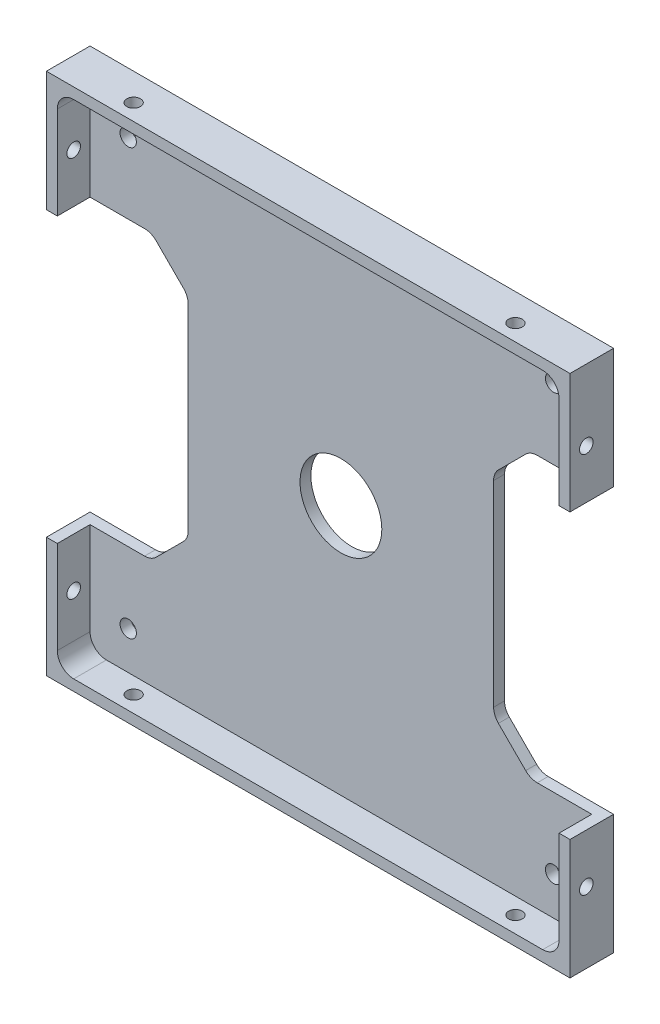
SolidWorks part; units mm, degrees
material "6061-T6 (SS)"
ref_plane "Front" through (0, 0, 0) normal (0, 0, 1) x (1, 0, 0)
ref_plane "Top" through (0, 0, 0) normal (0, 1, 0) x (1, 0, 0)
ref_plane "Right" through (0, 0, 0) normal (1, 0, 0) x (0, 0, -1)
sketch "Sketch1" plane through (0, 0, 0) normal (0, 0, 1) x (1, 0, 0)
  line L1 (-48, -48) -> (48, -48)
  line L2 (-48, -48) -> (-48, 48)
  line L3 (-48, 48) -> (48, 48)
  line L4 (48, -48) -> (48, 48)
  line L5 (-48, -48) -> (48, 48) construction
  line L6 (-48, 48) -> (48, -48) construction
  point P0 (0, 0)
  dimension "D1" = 96
  dimension "D2" = 96
extrude "Boss-Extrude1" add sketch "Sketch1" along normal blind 8
sketch "Sketch2" plane through (0, 0, 8) normal (0, 0, 1) x (1, 0, 0)
  line L1 (46, -46) -> (-46, -46)
  line L2 (46, -46) -> (46, 46)
  line L3 (46, 46) -> (-46, 46)
  line L4 (-46, -46) -> (-46, 46)
  line L5 (46, -46) -> (-46, 46) construction
  line L6 (46, 46) -> (-46, -46) construction
  point P0 (0, 0)
  dimension "D1" = 92
  dimension "D2" = 92
extrude "Component Platform" cut sketch "Sketch2" against normal blind 6
sketch "Sketch3" plane through (0, 0, 2) normal (0, 0, 1) x (1, 0, 0)
  line L1 (-33.8787, -25.1213) -> (-28.8787, -20.1213)
  line L2 (-33.8787, 25.1213) -> (-28.8787, 20.1213)
  line L3 (-28, -18) -> (-28, 18)
  line L4 (-48, -26) -> (-36, -26)
  line L7 (-48, 48) -> (-48, -48) construction
  line L8 (0, -56.7987) -> (0, 73.4321) construction
  line L9 (46, -46) -> (-57.8147, 57.8147) construction
  line L18 (46, 46) -> (-68.5705, -68.5705) construction
  line L23 (-48, 26) -> (-36, 26)
  line L26 (-48, -26) -> (-48, 26)
  line L28 (-48, -48) -> (48, -48) construction
  line L29 (48, -26) -> (48, 26)
  line L30 (48, 26) -> (36, 26)
  line L31 (33.8787, 25.1213) -> (28.8787, 20.1213)
  line L32 (28, -18) -> (28, 18)
  line L33 (33.8787, -25.1213) -> (28.8787, -20.1213)
  line L34 (48, -26) -> (36, -26)
  arc A3 (-28.8787, -20.1213) -> (-28, -18) centre (-31, -18) ccw
  arc A4 (-28.8787, 20.1213) -> (-28, 18) centre (-31, 18) cw
  arc A13 (-33.8787, -25.1213) -> (-36, -26) centre (-36, -23) cw
  arc A15 (-33.8787, 25.1213) -> (-36, 26) centre (-36, 23) ccw
  arc A17 (33.8787, 25.1213) -> (36, 26) centre (36, 23) cw
  arc A18 (28.8787, 20.1213) -> (28, 18) centre (31, 18) ccw
  arc A19 (28.8787, -20.1213) -> (28, -18) centre (31, -18) cw
  arc A20 (33.8787, -25.1213) -> (36, -26) centre (36, -23) ccw
  point P0 (-48, 0)
  point P37 (-48, 0)
  dimension "D2" = 3
  dimension "D3" = 3
  dimension "D4" = 20
  dimension "D6" = 3
  dimension "D7" = 3
  dimension "D8" = 135
  dimension "D5" = 52
  dimension "D9" = 135
  dimension "D10" = 12
  dimension "D11" = 12
  dimension "D12" = 48
extrude "Cable Slots" cut sketch "Sketch3" against normal mid plane 12
sketch "Sketch4" plane through (0, 0, 2) normal (0, 0, 1) x (1, 0, 0)
  circle A0 centre (0, 0) radius 7.5
  dimension "D1" = 15
extrude "Center Mass Cut" cut sketch "Sketch4" against normal blind 6
ref_plane "Center Y-Plane" through (0, 0, 0) normal (1, 0, 0) x (0, 0, -1)
ref_plane "Center X-Plane" through (0, 0, 0) normal (0, -1, 0) x (-1, 0, 0)
fillet "Inner Corner Fillets" radius 3 4 edges at (46, -46, 5) (-46, -46, 5) (46, 46, 5) (-46, 46, 5)
sketch "Sketch7" plane through (0, 0, 2) normal (0, 0, 1) x (1, 0, 0)
  line L1 (39, -39) -> (-39, -39)
  line L2 (39, -39) -> (39, 39)
  line L3 (39, 39) -> (-39, 39)
  line L4 (-39, -39) -> (-39, 39)
  line L5 (39, -39) -> (-39, 39) construction
  line L6 (39, 39) -> (-39, -39) construction
  point P0 (0, 0)
  dimension "D1" = 78
  dimension "D2" = 78
sketch "Sketch8" plane through (0, -48, 0) normal (0, -1, 0) x (-1, 0, 0)
  line L0 (48, -5) -> (-48, -5) construction
  line L1 (48, -8) -> (48, 0) construction
  line L2 (-48, -8) -> (-48, 0) construction
  line L3 (48, -8) -> (-48, -8) construction
  dimension "D1" = 3
sketch "Sketch9" plane through (48, 0, 0) normal (1, 0, 0) x (0, 0, -1)
  line L0 (-5, 48) -> (-5, -48) construction
  line L1 (-8, 48) -> (0, 48) construction
  line L2 (-8, -48) -> (0, -48) construction
  line L3 (-8, 26) -> (-8, 48) construction
  dimension "D1" = 3
hole_wizard "Tap Drill for M3x0.5 Tap1" positions "Sketch10" profile "Sketch11" hole size "M3x0.5" standard "ANSI Metric" end condition up to next
sketch "Sketch10" plane through (0, -48, 0) normal (0, -1, 0) x (-1, 0, 0)
  line L0 (48, -5) -> (-48, -5) construction
  point P0 (35, -5)
  point P4 (-35, -5)
  dimension "D1" = 70
  dimension "D2" = 35
sketch "Sketch11" plane through (-35, -48, 5) normal (1, 0, 0) x (0, 0, -1)
  line L0 (0, 0) -> (0, 2)
  line L1 (0, 2) -> (1.25, 2)
  line L2 (1.25, 2) -> (1.25, 0)
  line L5 (1.25, 0) -> (0, 0)
  line L11 (0, -6.35) -> (0, 107.95) construction
  dimension "Thru Hole Dia." = 2.5
  dimension "Thru Hole Depth" = 2
hole_wizard "Tap Drill for M3x0.5 Tap2" positions "Sketch12" profile "Sketch13" hole size "M3x0.5" standard "ANSI Metric" end condition up to next
sketch "Sketch12" plane through (48, 0, 0) normal (1, 0, 0) x (0, 0, -1)
  line L0 (-5, 48) -> (-5, -48) construction
  point P0 (-5, -35)
  point P4 (-5, 35)
  dimension "D1" = 70
  dimension "D2" = 35
sketch "Sketch13" plane through (48, -35, 5) normal (0, 1, 0) x (0, 0, -1)
  line L0 (0, 0) -> (0, 2)
  line L1 (0, 2) -> (1.25, 2)
  line L2 (1.25, 2) -> (1.25, 0)
  line L5 (1.25, 0) -> (0, 0)
  line L11 (0, -6.35) -> (0, 107.95) construction
  dimension "Thru Hole Dia." = 2.5
  dimension "Thru Hole Depth" = 2
mirror "Mirror1" about plane through (0, 0, 0) normal (0, -1, 0) of "Tap Drill for M3x0.5 Tap1"
mirror "Mirror2" about plane through (0, 0, 0) normal (1, 0, 0) of "Tap Drill for M3x0.5 Tap2"
hole_wizard "Ø3.0mm Dowel Hole3" positions "Sketch14" profile "Sketch15" hole size "Ø3.0" standard "ANSI Metric"
sketch "Sketch14" plane through (0, 0, 2) normal (0, 0, 1) x (1, 0, 0)
  point P0 (-39, -39)
  point P3 (39, -39)
  point P6 (39, 39)
  point P9 (-39, 39)
sketch "Sketch15" plane through (-39, -39, 2) normal (1, 0, 0) x (0, -1, 0)
  line L0 (0, 0) -> (0, 10.9013)
  line L1 (0, 10.9013) -> (1.5, 10)
  line L2 (1.5, 10) -> (1.5, 0)
  line L5 (1.5, 0) -> (0, 0)
  line L10 (0, 10.9013) -> (-1.5, 10) construction
  line L11 (0, -6.35) -> (0, 107.95) construction
  dimension "Hole Dia." = 3
  dimension "Hole Depth" = 10
  dimension "Drill Angle" = 118
